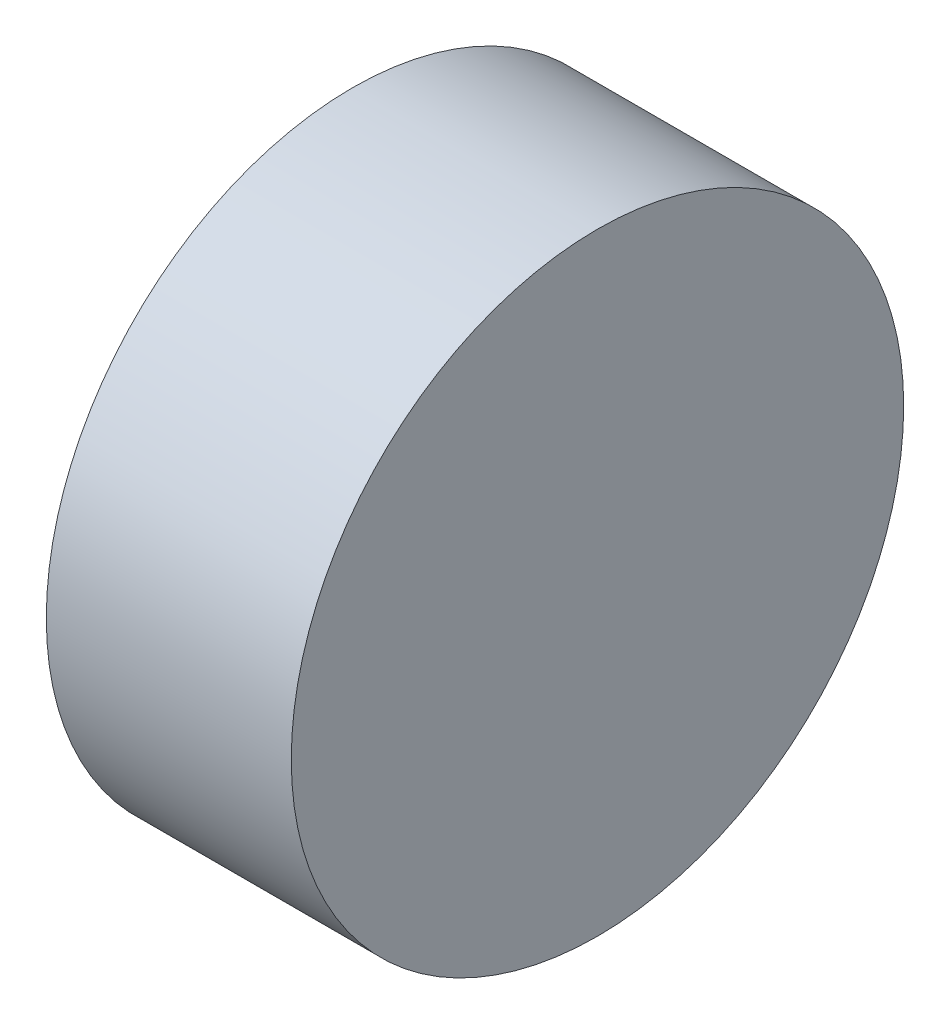
SolidWorks part; units mm, degrees
ref_plane "Спереди" through (0, 0, 0) normal (0, 0, 1) x (1, 0, 0)
ref_plane "Сверху" through (0, 0, 0) normal (0, 1, 0) x (1, 0, 0)
ref_plane "Справа" through (0, 0, 0) normal (1, 0, 0) x (0, 0, -1)
other "Configuration Table"
sketch "Sketch1" plane through (0, 0, 0) normal (0, 0, 1) x (1, 0, 0)
  line L1 (14.6277, -15.9309) -> (-5.3723, -15.9309)
  line L2 (14.6277, -15.9309) -> (14.6277, 9.0691)
  line L3 (14.6277, 9.0691) -> (-5.3723, 9.0691)
  line L4 (-5.3723, -15.9309) -> (-5.3723, 9.0691)
  line L5 (14.6277, -15.9309) -> (-5.3723, 9.0691) construction
  line L6 (14.6277, 9.0691) -> (-5.3723, -15.9309) construction
  point P0 (4.6277, -3.4309)
  dimension "D1" = 20
  dimension "D2" = 25
revolve "Revolve1" add sketch "Sketch1" angle 360 about L3
